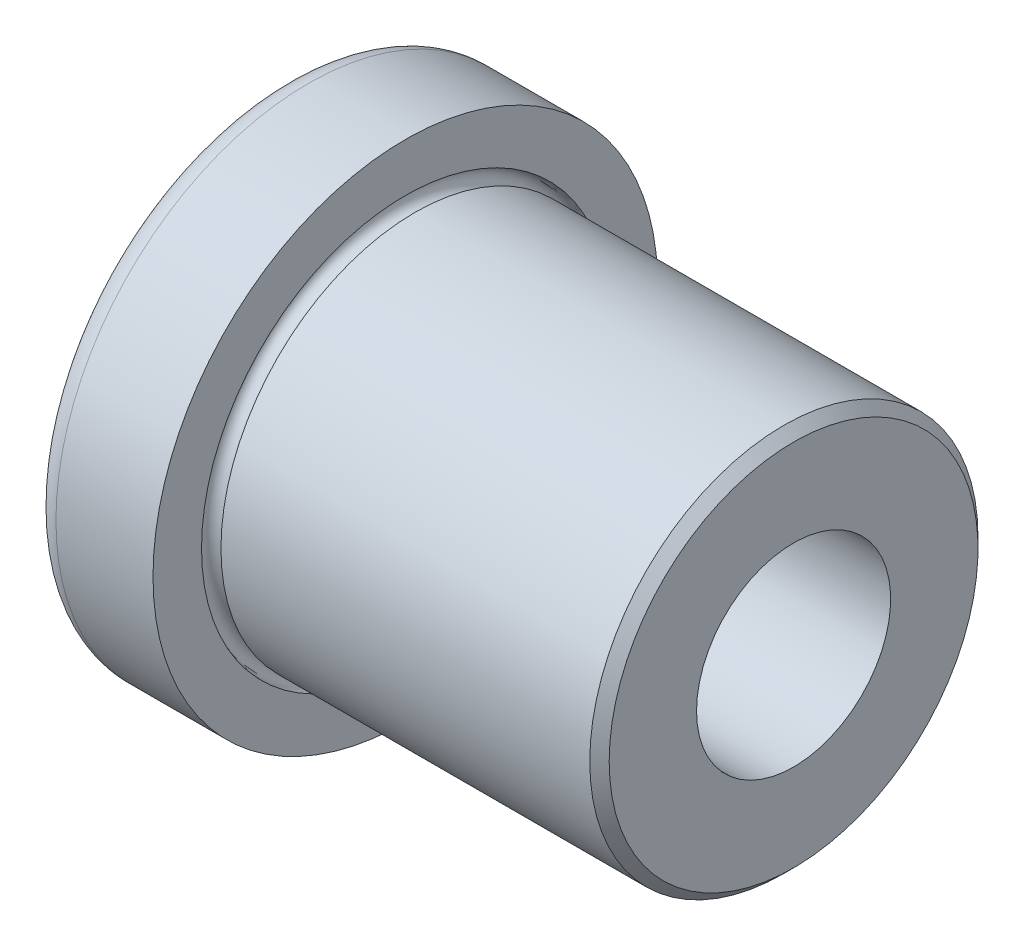
SolidWorks part; units mm, degrees
material "Alloy Steel"
ref_plane "Plane1" through (0, 0, 0) normal (0, 0, 1) x (1, 0, 0)
ref_plane "Plane2" through (0, 0, 0) normal (0, 1, 0) x (1, 0, 0)
ref_plane "Plane3" through (0, 0, 0) normal (1, 0, 0) x (0, 0, -1)
sketch "Sketch1" plane through (0, 0, 0) normal (0, 0, 1) x (1, 0, 0)
  line L0 (0, 0) -> (76.2, 0) construction
  line L1 (0, 3.9624) -> (0, 7.4676)
  line L2 (0.7874, 8.255) -> (3.9624, 8.255)
  line L3 (3.9624, 8.255) -> (3.9624, 6.6675)
  line L4 (4.2799, 6.35) -> (16.3449, 6.35)
  line L5 (16.3449, 6.35) -> (16.6624, 6.0325)
  line L6 (16.6624, 6.0325) -> (16.6624, 3.175)
  line L7 (16.6624, 3.175) -> (0.7874, 3.175)
  line L8 (16.3449, -6.35) -> (16.6624, -6.0325) construction
  line L9 (16.6624, -3.175) -> (0, -3.175) construction
  line L10 (4.2799, -6.35) -> (16.3449, -6.35) construction
  line L11 (0, -8.255) -> (3.9624, -8.255) construction
  arc A0 (3.9624, 6.6675) -> (4.2799, 6.35) centre (3.9624, 6.35) ccw
  arc A1 (0, 3.9624) -> (0.7874, 3.175) centre (0.7874, 3.9624) ccw
  arc A2 (0.7874, 8.255) -> (0, 7.4676) centre (0.7874, 7.4676) ccw
  point P20 (0, 3.175)
  point P23 (0, 8.255)
  dimension "Head_radii" = 0.7874
  dimension "D1" = 0.3175
  dimension "Hole_dia" = 6.35
  dimension "Body_dia" = 12.7
  dimension "Body_len" = 12.7
  dimension "Head_dia" = 16.51
  dimension "Head_ht" = 3.9624
  dimension "D2" = 12.065
  dimension "D3" = 45
revolve "BaseBody" add sketch "Sketch1" angle 360 about L0
sketch "Sketch4" plane through (0, 0, 0) normal (0, 0, 1) x (1, 0, 0)
  line L0 (0.7874, 8.255) -> (3.9624, 7.62)
  line L1 (3.9624, -8.255) -> (3.9624, 8.255) construction
  line L2 (3.9624, 7.62) -> (3.9624, 8.255)
  line L3 (3.9624, 8.255) -> (0.7874, 8.255)
  dimension "D1" = 0.635
revolve "Cut-Revolve1" [suppressed] cut sketch "Sketch4" angle 360
equation "\"D1@Sketch1\" =  ( \"Body_dia@Sketch1\" -  ( \"Body_dia@Sketch1\" * .9 )  )  / 4"
equation "\"D2@Sketch1\" = \"Body_dia@Sketch1\" -  ( \"D1@Sketch1\" * 2 ) "
